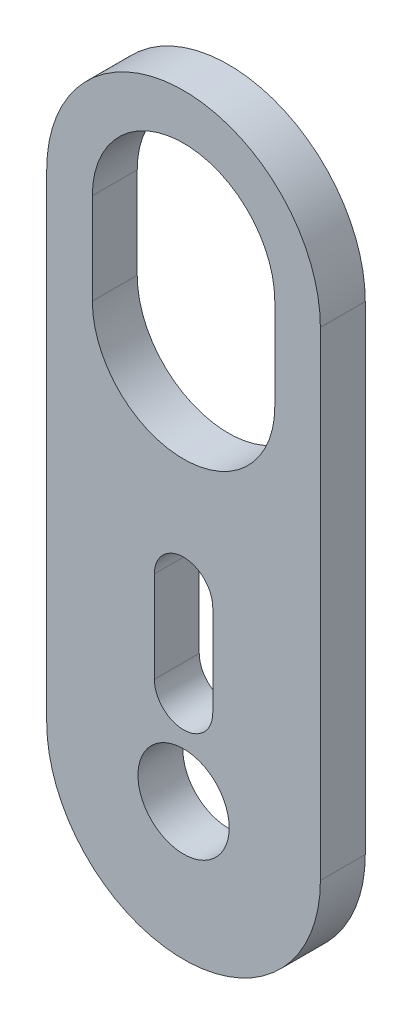
SolidWorks part; units mm, degrees
ref_plane "Alzado" through (0, 0, 0) normal (0, 0, 1) x (1, 0, 0)
ref_plane "Planta" through (0, 0, 0) normal (0, 1, 0) x (1, 0, 0)
ref_plane "Vista lateral" through (0, 0, 0) normal (1, 0, 0) x (0, 0, -1)
sketch "Croquis1" plane through (0, 0, 0) normal (0, 0, 1) x (1, 0, 0)
  line L0 (0, 0) -> (0, 33.3375) construction
  line L3 (-9.525, 0) -> (-9.525, 33.3375)
  line L6 (9.525, 0) -> (9.525, 33.3375)
  line L9 (0, 6.35) -> (0, 12.7) construction
  line L10 (-2.032, 6.35) -> (-2.032, 12.7)
  line L11 (2.032, 6.35) -> (2.032, 12.7)
  line L12 (0, 33.3375) -> (0, 26.9875) construction
  line L13 (6.35, 33.3375) -> (6.35, 26.9875)
  line L14 (-6.35, 33.3375) -> (-6.35, 26.9875)
  arc A8 (-9.525, 0) -> (9.525, 0) centre (0, 0) ccw
  arc A9 (9.525, 33.3375) -> (-9.525, 33.3375) centre (0, 33.3375) ccw
  circle A10 centre (0, 0) radius 3.175
  arc A11 (-2.032, 6.35) -> (2.032, 6.35) centre (0, 6.35) ccw
  arc A12 (2.032, 12.7) -> (-2.032, 12.7) centre (0, 12.7) ccw
  arc A13 (6.35, 33.3375) -> (-6.35, 33.3375) centre (0, 33.3375) ccw
  arc A14 (-6.35, 26.9875) -> (6.35, 26.9875) centre (0, 26.9875) ccw
  point P2 (0, 16.6687)
  point P12 (0, 9.525)
  point P17 (0, 30.1625)
  point P24 (0, 39.6516)
  dimension "D2" = 6.35
  dimension "D1" = 6.35
  dimension "D3" = 2.032
  dimension "D4" = 6.35
  dimension "D7" = 9.525
  dimension "D5" = 6.35
  dimension "D6" = 26.9875
  dimension "D8" = 12.7
  dimension "D9" = 3.175
extrude "Saliente-Extruir1" add sketch "Croquis1" along normal blind 3.1242
